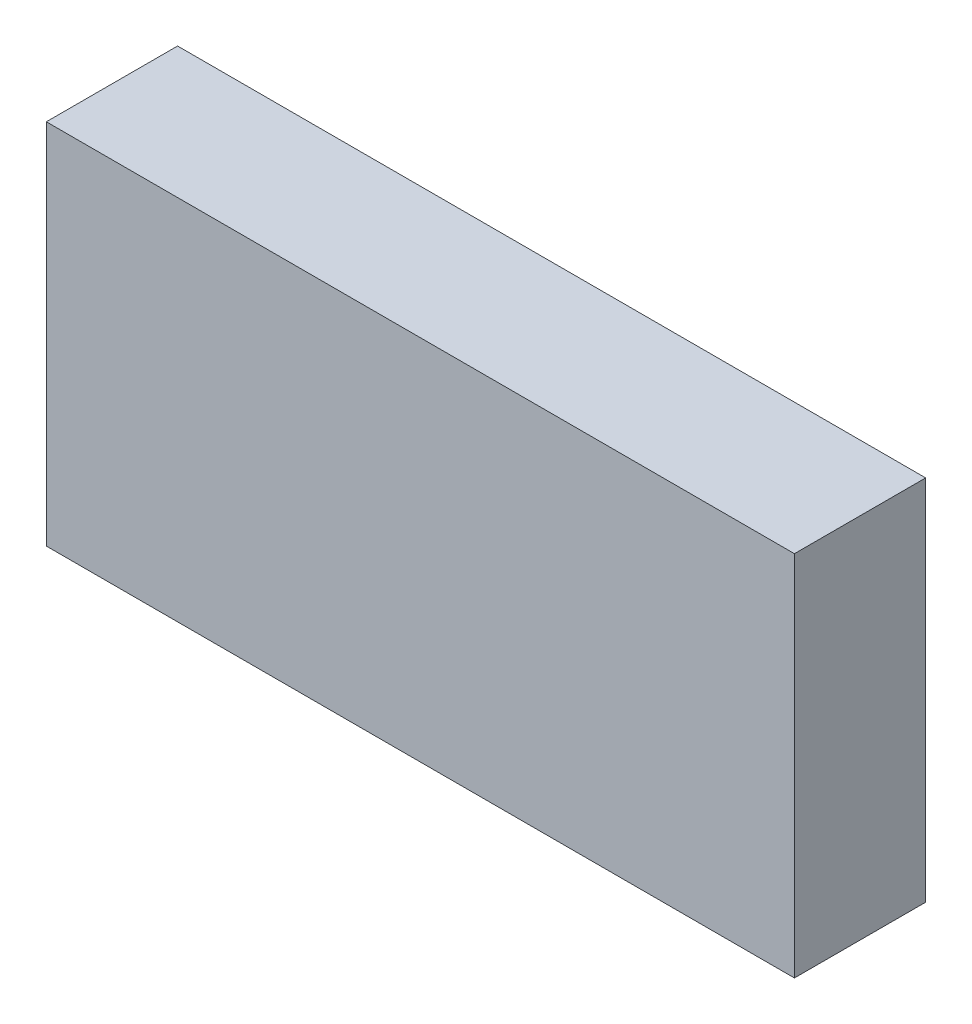
SolidWorks part; units mm, degrees
ref_plane "前视基准面" through (0, 0, 0) normal (0, 0, 1) x (1, 0, 0)
ref_plane "上视基准面" through (0, 0, 0) normal (0, 1, 0) x (1, 0, 0)
ref_plane "右视基准面" through (0, 0, 0) normal (1, 0, 0) x (0, 0, -1)
other "Configuration Table"
sketch "草图1" plane through (0, 0, 0) normal (0, 0, 1) x (1, 0, 0)
  line L1 (28.5, -14) -> (-28.5, -14)
  line L2 (28.5, -14) -> (28.5, 14)
  line L3 (28.5, 14) -> (-28.5, 14)
  line L4 (-28.5, -14) -> (-28.5, 14)
  line L5 (28.5, -14) -> (-28.5, 14) construction
  line L6 (28.5, 14) -> (-28.5, -14) construction
  point P0 (0, 0)
  dimension "D1" = 57
  dimension "D2" = 28
extrude "凸台-拉伸1" add sketch "草图1" along normal blind 10
